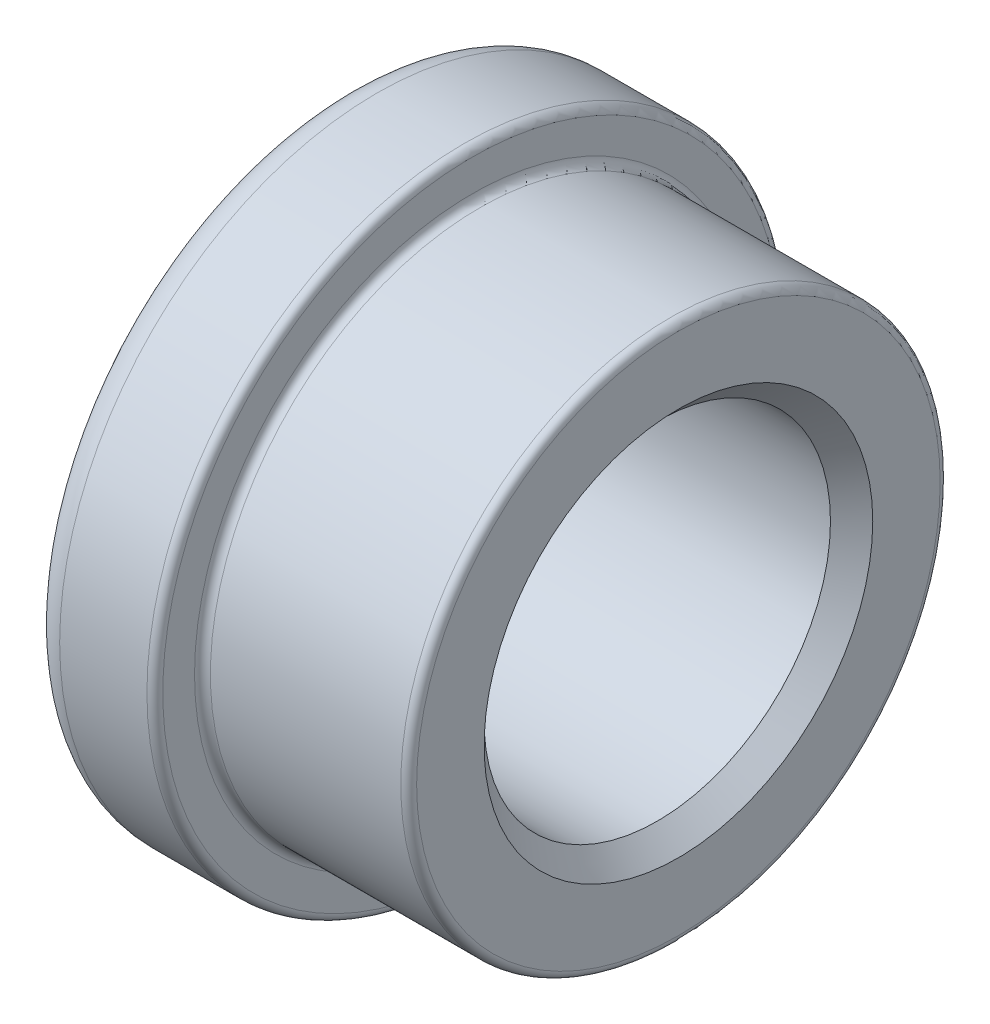
SolidWorks part; units mm, degrees
ref_plane "Plane1" through (0, 0, 0) normal (0, 0, 1) x (1, 0, 0)
ref_plane "Plane2" through (0, 0, 0) normal (0, 1, 0) x (1, 0, 0)
ref_plane "Plane3" through (0, 0, 0) normal (1, 0, 0) x (0, 0, -1)
sketch "Sketch1" plane through (0, 0, 0) normal (0, 0, 1) x (1, 0, 0)
  line L0 (0, 12.25) -> (0, 16.5)
  line L1 (-0.5, 17) -> (-12.5, 17)
  line L2 (-21, 18) -> (-21, 12.25)
  line L3 (-21, 12.25) -> (-19.6675, 10.9175)
  line L4 (-1.3325, 10.9175) -> (0, 12.25)
  line L5 (-13, 17.5) -> (-13, 19.5)
  line L6 (-13.5, 20) -> (-19, 20)
  line L12 (-19.6675, 10.9175) -> (-1.3325, 10.9175)
  line L13 (0, 0) -> (-20, 0) construction
  arc A0 (-19, 20) -> (-21, 18) centre (-19, 18) ccw
  arc A1 (-12.5, 17) -> (-13, 17.5) centre (-12.5, 17.5) cw
  arc A2 (-13.5, 20) -> (-13, 19.5) centre (-13.5, 19.5) cw
  arc A3 (-0.5, 17) -> (0, 16.5) centre (-0.5, 16.5) cw
  point P0 (0, 10.9175)
  point P12 (-21, 10.9175)
  dimension "D5" = 2
  dimension "D11" = 0.5
  dimension "D2" = 45
  dimension "D3" = 34
  dimension "D4" = 21.835
  dimension "D6" = 24.5
  dimension "D7" = 45
  dimension "D8" = 21
  dimension "D9" = 13
  dimension "D10" = 40
  dimension "D12" = 24.5
revolve "Base-Revolve" add sketch "Sketch1" angle 360 about L13
cosmetic thread "Cosmetic Thread1" parameters "D2"=24
